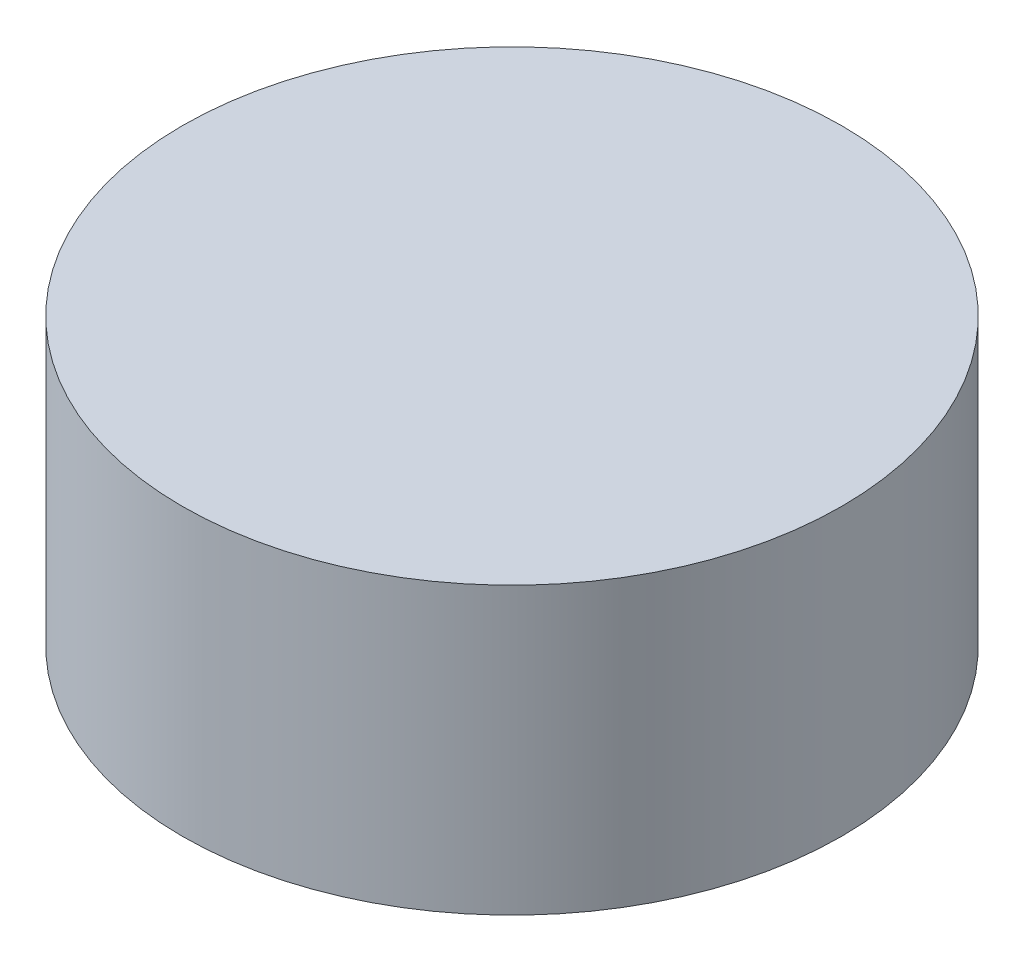
SolidWorks part; units mm, degrees
ref_plane "Front Plane" through (0, 0, 0) normal (0, 0, 1) x (1, 0, 0)
ref_plane "Top Plane" through (0, 0, 0) normal (0, 1, 0) x (1, 0, 0)
ref_plane "Right Plane" through (0, 0, 0) normal (1, 0, 0) x (0, 0, -1)
sketch "Sketch2" plane through (0, 0, 0) normal (0, 1, 0) x (1, 0, 0)
  circle A0 centre (0, 0) radius 1500
  dimension "D1" = 3000
extrude "Boss-Extrude1" add sketch "Sketch2" along normal blind 1300
shell "Shell4" thickness 100
